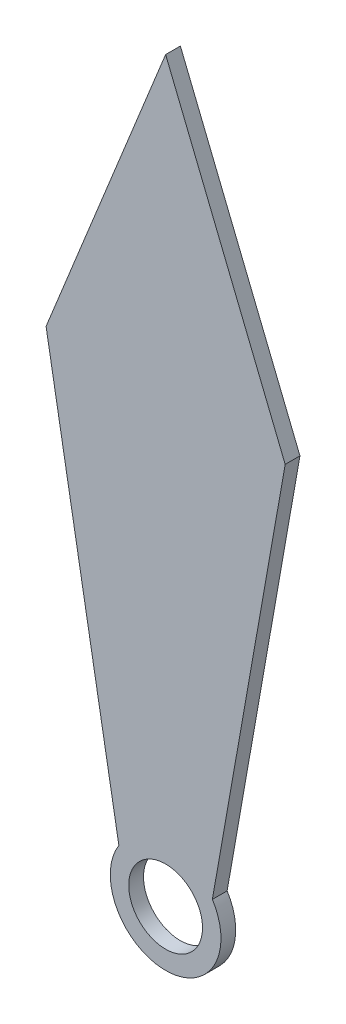
SolidWorks part; units mm, degrees
ref_plane "Alzado" through (0, 0, 0) normal (0, 0, 1) x (1, 0, 0)
ref_plane "Planta" through (0, 0, 0) normal (0, 1, 0) x (1, 0, 0)
ref_plane "Vista lateral" through (0, 0, 0) normal (1, 0, 0) x (0, 0, -1)
sketch "Croquis1" plane through (0, 0, 0) normal (0, 0, 1) x (1, 0, 0)
  line L0 (0, 0) -> (0, 10) construction
  line L1 (-0.6336, 0.4013) -> (-1.6202, 6)
  line L2 (-1.6202, 6) -> (0, 10)
  line L3 (0.6336, 0.4013) -> (1.6202, 6)
  line L4 (1.6202, 6) -> (0, 10)
  circle A0 centre (0, 0) radius 0.5
  circle A1 centre (0, 0) radius 0.75
  dimension "D2" = 1
  dimension "D3" = 1.5
  dimension "D1" = 10
  dimension "D4" = 4
extrude "Saliente-Extruir2" add sketch "Croquis1" along normal blind 0.2
